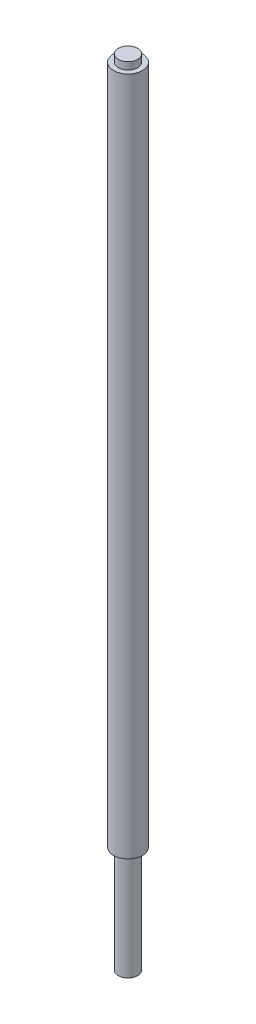
SolidWorks part; units mm, degrees
material "AISI 321 Annealed Stainless Steel (SS)"
ref_plane "Front Plane" through (0, 0, 0) normal (0, 0, 1) x (1, 0, 0)
ref_plane "Top Plane" through (0, 0, 0) normal (0, 1, 0) x (1, 0, 0)
ref_plane "Right Plane" through (0, 0, 0) normal (1, 0, 0) x (0, 0, -1)
sketch "Sketch1" plane through (0, 0, 0) normal (0, 1, 0) x (1, 0, 0)
  circle A0 centre (0, 0) radius 4
  dimension "D1" = 8
extrude "Boss-Extrude1" add sketch "Sketch1" along normal blind 329.2 contours A0
ref_plane "Plane1" through (0, 326.2, 0) normal (0, 1, 0) x (1, 0, 0)
sketch "Sketch2" plane through (0, 326.2, 0) normal (0, 1, 0) x (1, 0, 0)
  circle A0 centre (0, 0) radius 6
  dimension "D1" = 12
extrude "Boss-Extrude2" add sketch "Sketch2" against normal blind 282
ref_plane "Plane2" through (0, 289.2, 0) normal (0, 1, 0) x (1, 0, 0)
sketch "Sketch4" plane through (0, 289.2, 0) normal (0, 1, 0) x (1, 0, 0)
  circle A0 centre (0, 0) radius 4
  circle A1 centre (0, 0) radius 5
  dimension "D1" = 8
  dimension "D2" = 10
extrude "Cut-Extrude1" cut sketch "Sketch4" against normal blind 30
